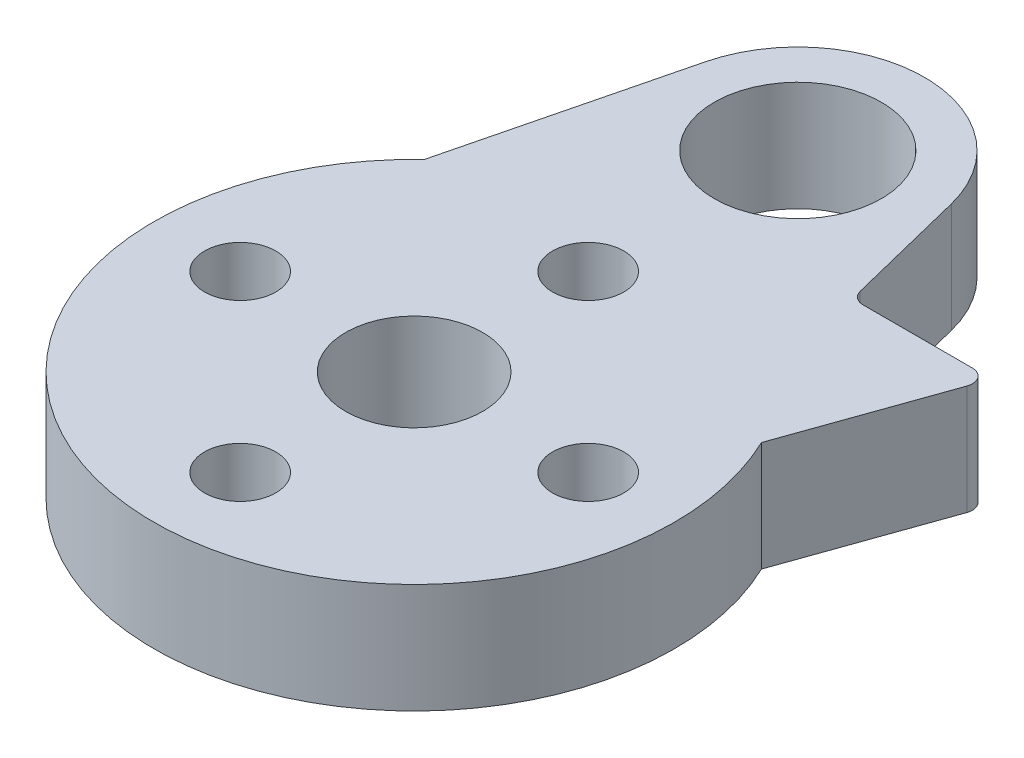
SolidWorks part; units mm, degrees
material "Tough 2000"
ref_plane "Front Plane" through (0, 0, 0) normal (0, 0, 1) x (1, 0, 0)
ref_plane "Top Plane" through (0, 0, 0) normal (0, 1, 0) x (1, 0, 0)
ref_plane "Right Plane" through (0, 0, 0) normal (1, 0, 0) x (0, 0, -1)
sketch "Sketch1" plane through (0, 0, 0) normal (0, 1, 0) x (1, 0, 0)
  line L1 (-4.4887, 15.1149) -> (-7.7641, 1.9285)
  line L2 (4.4887, 15.1149) -> (7.7641, 1.9285)
  arc A0 (-7.7641, 1.9285) -> (7.7641, 1.9285) centre (0, 0) ccw
  arc A1 (4.4887, 15.1149) -> (-4.4887, 15.1149) centre (0, 14) ccw
  circle A2 centre (0, 14) radius 3.05
  circle A3 centre (0, 0) radius 2.5
  dimension "D1" = 14
  dimension "D2" = 4.6251
  dimension "D3" = 8
extrude "Boss-Extrude1" add sketch "Sketch1" along normal blind 4
sketch "Sketch2" plane through (0, 4, 0) normal (0, 1, 0) x (1, 0, 0)
  line L0 (0, 0) -> (0, 6.35) construction
  circle A0 centre (0, 6.35) radius 1.3
  circle A1 centre (6.35, 0) radius 1.3
  circle A2 centre (0, -6.35) radius 1.3
  circle A3 centre (-6.35, 0) radius 1.3
  point P13 (0, 0)
  dimension "D1" = 4
extrude "Cut-Extrude1" cut sketch "Sketch2" against normal blind 4
sketch "Sketch3" plane through (0, 4, 0) normal (0, 1, 0) x (1, 0, 0)
  circle A4 centre (0, 0) radius 7.65
  arc A5 (-1.5493, 9.3728) -> (1.5493, 9.3728) centre (0, 0) ccw
  arc A6 (-1.5493, 9.3728) -> (1.5493, 9.3728) centre (0, 14) ccw
extrude "Boss-Extrude2" add sketch "Sketch3" against normal blind 4
sketch "Sketch4" plane through (0, 4, 0) normal (0, 1, 0) x (1, 0, 0)
  line L25 (10.7672, 10.3095) -> (8.5672, 4.1053)
  line L26 (10.7672, 10.3095) -> (5.6823, 10.3095)
  line L27 (6.529, 6.9009) -> (4.4887, 15.1149) construction
  line L29 (2.1651, 1.25) -> (8.5672, 4.1053)
  line L30 (5.6823, 10.3095) -> (1.7931, 1.7421)
  arc A3 (2.1651, 1.25) -> (1.7931, 1.7421) centre (0, 0) ccw
  arc A5 (-6.529, 6.9009) -> (6.529, 6.9009) centre (0, 0) ccw construction
extrude "Boss-Extrude3" add sketch "Sketch4" against normal up to surface (4 mm away) up to face at (0, 0, -7.7852)
fillet "Fillet9" radius 0.5 2 edges at (5.6823, 2, -10.3095) (10.7672, 2, -10.3095)
